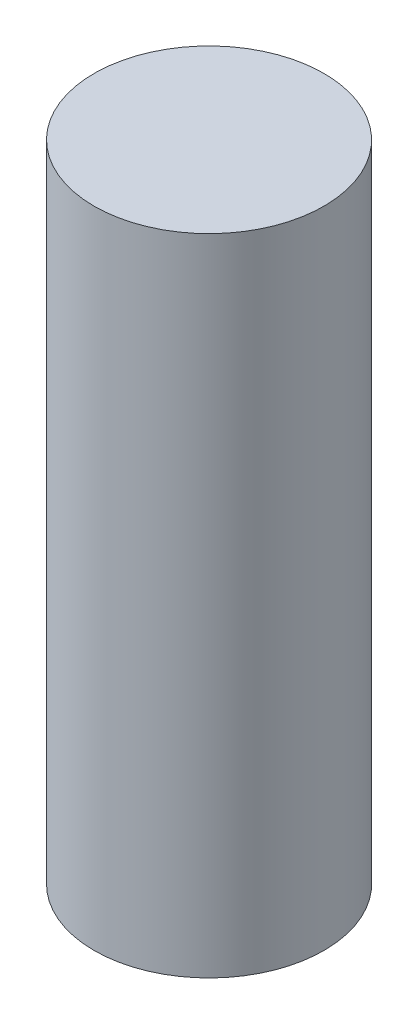
SolidWorks part; units mm, degrees
ref_plane "Front Plane" through (0, 0, 0) normal (0, 0, 1) x (1, 0, 0)
ref_plane "Top Plane" through (0, 0, 0) normal (0, 1, 0) x (1, 0, 0)
ref_plane "Right Plane" through (0, 0, 0) normal (1, 0, 0) x (0, 0, -1)
sketch "Sketch1" plane through (0, 0, 0) normal (0, 1, 0) x (1, 0, 0)
  circle A0 centre (0, 0) radius 2.675
  dimension "D1" = 5.35
extrude "Boss-Extrude1" add sketch "Sketch1" along normal blind 15
